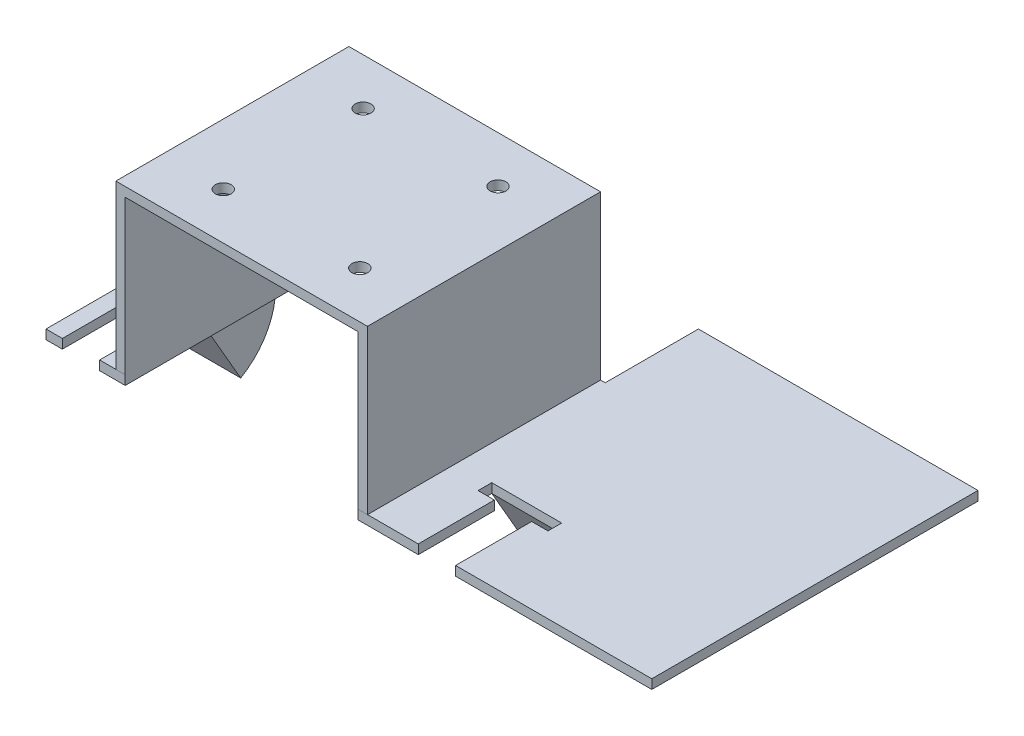
SolidWorks part; units mm, degrees
ref_plane "Front Plane" through (0, 0, 0) normal (0, 0, 1) x (1, 0, 0)
ref_plane "Top Plane" through (0, 0, 0) normal (0, 1, 0) x (1, 0, 0)
ref_plane "Right Plane" through (0, 0, 0) normal (1, 0, 0) x (0, 0, -1)
sketch "Sketch2" plane through (0, 0, 0) normal (0, 1, 0) x (1, 0, 0)
  line L1 (-106.6991, 41.4756) -> (23.3009, 41.4756)
  line L2 (-106.6991, 41.4756) -> (-106.6991, -28.5244)
  line L3 (-106.6991, -28.5244) -> (23.3009, -28.5244)
  line L4 (23.3009, 41.4756) -> (23.3009, -28.5244)
  line L5 (-106.6991, 41.4756) -> (23.3009, -28.5244) construction
  line L6 (-106.6991, -28.5244) -> (23.3009, 41.4756) construction
  point P0 (-41.6991, 6.4756)
  dimension "D1" = 70
  dimension "D2" = 130
extrude "Boss-Extrude1" add sketch "Sketch2" along normal blind 2 contours L2 L1 L4 L3
sketch "Sketch3" plane through (0, 2, 0) normal (0, 1, 0) x (1, 0, 0)
  line L1 (-91.6991, 41.4613) -> (-37.6991, 41.4613)
  line L2 (-91.6991, 41.4613) -> (-91.6991, -28.5387)
  line L3 (-91.6991, -28.5387) -> (-37.6991, -28.5387)
  line L4 (-37.6991, 41.4613) -> (-37.6991, -28.5387)
  line L5 (-91.6991, 41.4613) -> (-37.6991, -28.5387) construction
  line L6 (-91.6991, -28.5387) -> (-37.6991, 41.4613) construction
  line L7 (23.3009, 41.4756) -> (23.3009, -28.5244) construction
  point P0 (-54.989, 41.4756)
  dimension "D1" = 70
  dimension "D2" = 54
  dimension "D3" = 61
extrude "Boss-Extrude2" add sketch "Sketch3" along normal blind 35
sketch "Sketch4" plane through (0, 2, 0) normal (0, 1, 0) x (1, 0, 0)
  line L0 (-37.6991, 41.4613) -> (-91.6991, 41.4613) construction
  line L1 (-89.6991, 41.4613) -> (-39.6991, 41.4613)
  line L2 (-89.6991, 41.4613) -> (-89.6991, -28.5387)
  line L3 (-89.6991, -28.5387) -> (-39.6991, -28.5387)
  line L4 (-39.6991, 41.4613) -> (-39.6991, -28.5387)
  line L5 (-91.6991, -28.5387) -> (-37.6991, -28.5387) construction
  line L6 (-37.6991, -28.5244) -> (-37.6991, 41.4613) construction
  line L7 (-91.6991, 41.4613) -> (-91.6991, -28.5244) construction
  dimension "D1" = 2
  dimension "D2" = 2
extrude "Cut-Extrude2" cut sketch "Sketch4" along normal blind 33 and the other way blind 2
sketch "Sketch6" plane through (0, 0, -41.4756) normal (0, 0, -1) x (-1, 0, 0)
  line L1 (39.6991, 2) -> (89.6991, 2)
  line L2 (39.6991, 2) -> (39.6991, 0)
  line L3 (39.6991, 0) -> (89.6991, 0)
  line L4 (89.6991, 2) -> (89.6991, 0)
extrude "Cut-Extrude3" cut sketch "Sketch6" against normal blind 33
sketch "Sketch7" plane through (0, 0, 0) normal (0, -1, 0) x (1, 0, 0)
  line L0 (23.3009, -41.4756) -> (23.3009, 28.5244) construction
  line L1 (-106.6991, -41.4756) -> (-36.6991, -41.4756)
  line L2 (-106.6991, -41.4756) -> (-106.6991, -21.4756)
  line L3 (-106.6991, -21.4756) -> (-36.6991, -21.4756)
  line L4 (-36.6991, -41.4756) -> (-36.6991, -21.4756)
  dimension "D1" = 20
  dimension "D2" = 60
extrude "Cut-Extrude4" cut sketch "Sketch7" against normal blind 40
sketch "Sketch8" plane through (0, 0, 0) normal (0, -1, 0) x (1, 0, 0)
  line L1 (-7.6991, 26.2244) -> (-4.6991, 26.2244)
  line L2 (-7.6991, 26.2244) -> (-7.6991, 18.2244)
  line L3 (-7.6991, 18.2244) -> (-4.6991, 18.2244)
  line L4 (-4.6991, 26.2244) -> (-4.6991, 18.2244)
  line L5 (-39.6991, 28.5387) -> (-39.6991, -21.4756) construction
  line L6 (-39.6991, 28.5244) -> (23.3009, 28.5244) construction
  dimension "D1" = 35
  dimension "D2" = 3
  dimension "D3" = 8
  dimension "D4" = 10.3
hole_wizard "M3 Clearance Hole4" positions "Sketch19" profile "Sketch20" hole size "M3" standard "ANSI Metric"
sketch "Sketch19" plane through (0, 35, 0) normal (0, -1, 0) x (-1, 0, 0)
  line L0 (89.6991, -28.5387) -> (39.6991, -28.5387) construction
  line L1 (39.6991, -28.5387) -> (39.6991, 21.4756) construction
  line L2 (89.6991, 21.4756) -> (39.6991, 21.4756) construction
  point P0 (49.3396, -18.5387)
  point P2 (49.6991, 11.4756)
  point P4 (78.6537, -18.5387)
  point P6 (78.6537, 11.4756)
  dimension "D1" = 10
  dimension "D2" = 10
  dimension "D3" = 10
sketch "Sketch20" plane through (-49.3396, 35, 18.5387) normal (1, 0, 0) x (0, 0, -1)
  line L0 (0, 0) -> (0, 4.5215)
  line L1 (0, 4.5215) -> (1.7, 3.5)
  line L2 (1.7, 3.5) -> (1.7, 0)
  line L5 (1.7, 0) -> (0, 0)
  line L10 (0, 4.5215) -> (-1.7, 3.5) construction
  line L11 (0, -6.35) -> (0, 107.95) construction
  dimension "Hole Dia." = 3.4
  dimension "Hole Depth" = 3.5
  dimension "Drill Angle" = 118
sketch "Sketch21" plane through (0, 0, 0) normal (0, -1, 0) x (1, 0, 0)
  line L0 (-39.6991, 28.5244) -> (23.3009, 28.5244) construction
  line L1 (-30.3113, 9.2544) -> (-15.3113, 9.2544)
  line L2 (-30.3113, 9.2544) -> (-30.3113, -5.7456)
  line L3 (-30.3113, -5.7456) -> (-15.3113, -5.7456)
  line L4 (-15.3113, 9.2544) -> (-15.3113, -5.7456)
  dimension "D1" = 15
  dimension "D2" = 15
  dimension "D3" = 19.27
revolve "Revolve1" add sketch "Sketch21" angle 60 about L1
sketch "Sketch22" plane through (0, 0, 0) normal (0, -1, 0) x (1, 0, 0)
  line L1 (-30.3113, 9.2544) -> (-15.3113, 9.2544)
  line L2 (-30.3113, 9.2544) -> (-30.3113, 12.1957)
  line L3 (-30.3113, 12.1957) -> (-15.3113, 12.1957)
  line L4 (-15.3113, 9.2544) -> (-15.3113, 12.1957)
  line L5 (-15.3113, -5.7456) -> (-15.3113, 9.2544) construction
  line L6 (-30.3113, 9.2544) -> (-30.3113, -5.7456) construction
extrude "Cut-Extrude6" cut sketch "Sketch22" against normal blind 55
sketch "Sketch23" plane through (0, 0, 0) normal (0, -1, 0) x (1, 0, 0)
  line L0 (-39.6991, 28.5244) -> (23.3009, 28.5244) construction
  line L1 (-26.8113, 28.5244) -> (-18.8113, 28.5244)
  line L2 (-26.8113, 28.5244) -> (-26.8113, 12.1957)
  line L3 (-26.8113, 12.1957) -> (-18.8113, 12.1957)
  line L4 (-18.8113, 28.5244) -> (-18.8113, 12.1957)
  line L5 (-15.3113, 12.1957) -> (-30.3113, 12.1957) construction
  line L6 (-30.3113, 12.1957) -> (-30.3113, 9.2544) construction
  dimension "D1" = 8
  dimension "D2" = 3.5
extrude "Cut-Extrude7" cut sketch "Sketch23" against normal blind 55
ref_plane "Plane10" through (-60.9991, 0, 0) normal (-1, 0, 0) x (0, 0, 1)
mirror "Mirror1" about plane through (-60.9991, 0, 0) normal (-1, 0, 0) of "Revolve1"
mirror "Mirror2" about plane through (-60.9991, 0, 0) normal (-1, 0, 0) of "Cut-Extrude7", "Cut-Extrude6"
